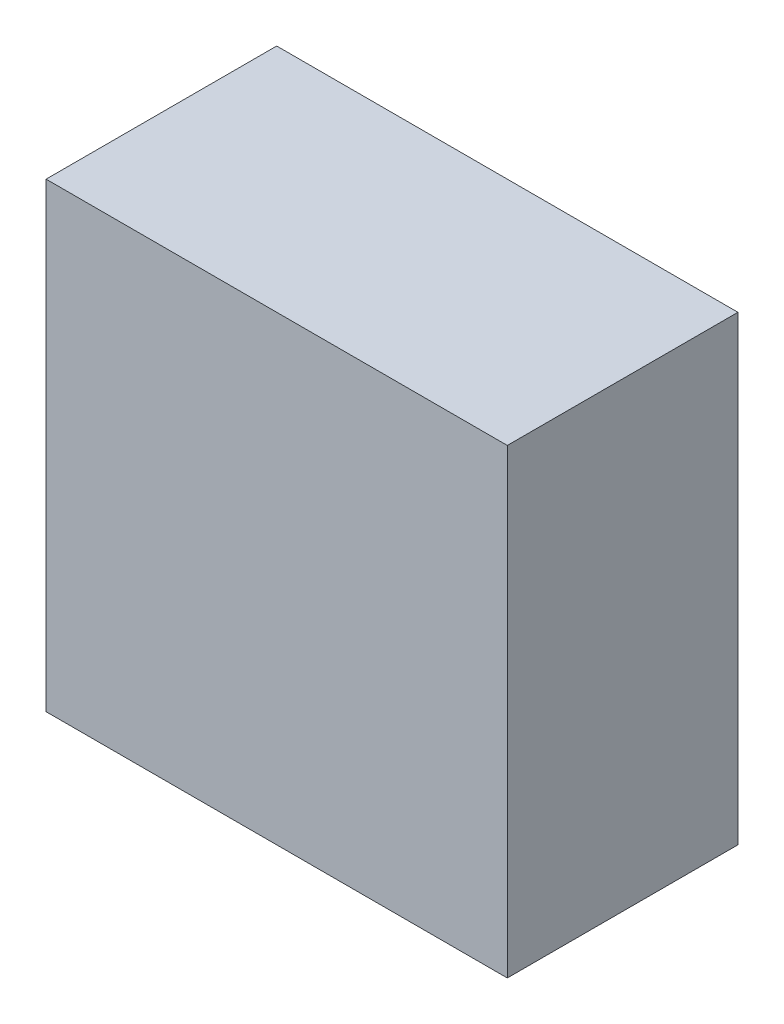
SolidWorks part; units mm, degrees
ref_plane "Front Plane" through (0, 0, 0) normal (0, 0, 1) x (1, 0, 0)
ref_plane "Top Plane" through (0, 0, 0) normal (0, 1, 0) x (1, 0, 0)
ref_plane "Right Plane" through (0, 0, 0) normal (1, 0, 0) x (0, 0, -1)
sketch "Sketch1" plane through (0, 0, 0) normal (0, 0, 1) x (1, 0, 0)
  line L1 (0, 0) -> (25.4, 0)
  line L2 (0, 0) -> (0, -25.4)
  line L3 (0, -25.4) -> (25.4, -25.4)
  line L4 (25.4, 0) -> (25.4, -25.4)
  dimension "D1" = 25.4
  dimension "D2" = 25.4
extrude "Boss-Extrude1" add sketch "Sketch1" along normal blind 12.7
